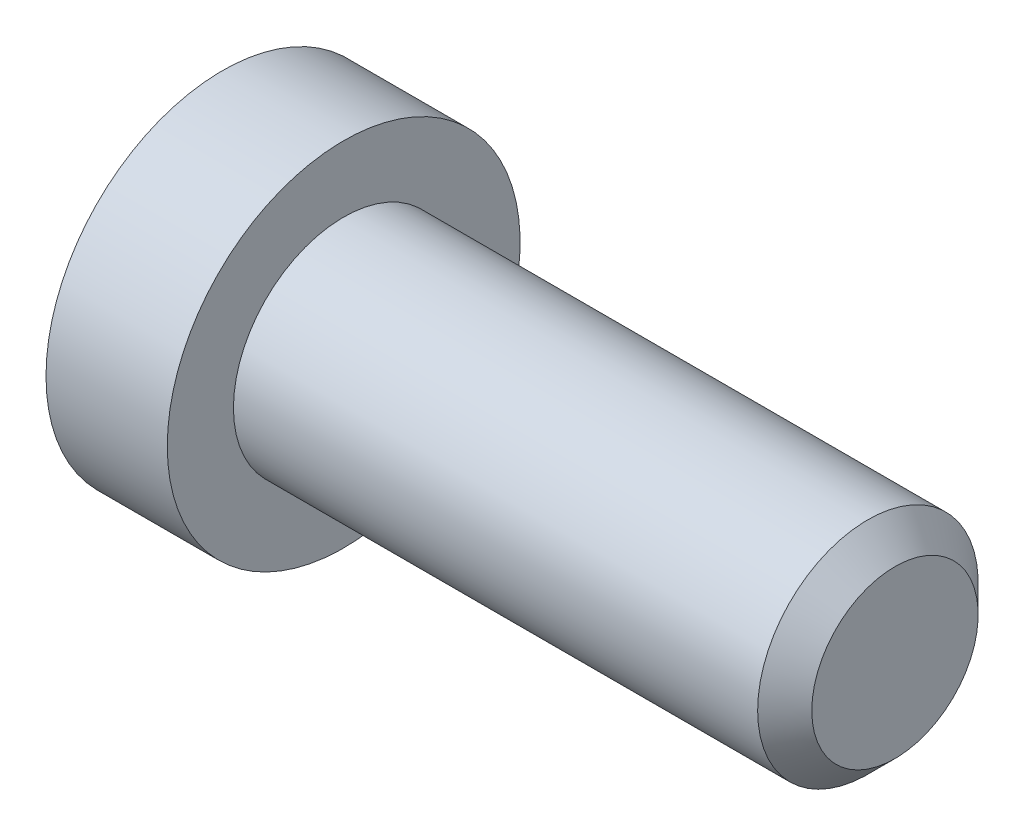
SolidWorks part; units mm, degrees
material "AISI 304"
ref_plane "正面" through (0, 0, 0) normal (0, 0, 1) x (1, 0, 0)
ref_plane "平面" through (0, 0, 0) normal (0, 1, 0) x (1, 0, 0)
ref_plane "右側面" through (0, 0, 0) normal (1, 0, 0) x (0, 0, -1)
ref_plane "Plane1" through (0, 0, 0) normal (0, 0, 1) x (1, 0, 0)
sketch "Sketch1" plane through (0, 0, 0) normal (0, 0, 1) x (1, 0, 0)
  line L0 (0, 0) -> (0, 1)
  line L1 (0, 1) -> (4.7545, 1)
  line L2 (4.7545, 1) -> (5, 0.7545)
  line L3 (5, 0.7545) -> (5, 0)
  line L4 (5, 0) -> (0, 0)
  line L5 (5, 0) -> (0, 0) construction
revolve "Revolve1" add sketch "Sketch1" angle 360 about L5
cosmetic thread "Cosmetic Thread1" parameters "D1"=3.8, "D2"=1.509
ref_plane "Plane2" through (0, 0, 0) normal (0, 0, 1) x (1, 0, 0)
sketch "Sketch2" plane through (0, 0, 0) normal (0, 0, 1) x (1, 0, 0)
  line L0 (-1.1, 0) -> (-1.1, 1.6)
  line L1 (-1.1, 1.6) -> (0, 1.6)
  line L2 (0, 1.6) -> (0, 0)
  line L3 (0, 0) -> (-1.1, 0)
  line L4 (0, 0) -> (-1.1, 0) construction
revolve "Revolve2" add sketch "Sketch2" angle 360 about L4
ref_plane "Plane3" through (0, 0, 0) normal (0, 0, 1) x (1, 0, 0)
sketch "Sketch3" plane through (0, 0, 0) normal (0, 0, 1) x (1, 0, 0)
  line L0 (-1.1, 0) -> (-1.1, 0.78)
  line L1 (-1.1, 0.78) -> (-0.97, 0.65)
  line L2 (-0.97, 0.65) -> (0.1, 0.65)
  line L3 (0.1, 0.65) -> (0.4753, 0)
  line L4 (0.4753, 0) -> (-1.1, 0)
  line L5 (0.4753, 0) -> (-1.1, 0) construction
revolve "Cut-Revolve1" cut sketch "Sketch3" angle 360 about L5
ref_plane "Plane4" through (-1.1, 0, 0) normal (1, 0, 0) x (0, 0, -1)
sketch "Sketch4" plane through (-1.1, 0, 0) normal (1, 0, 0) x (0, 0, -1)
  line L0 (-0.65, -0.3753) -> (0, -0.7506)
  line L1 (0, -0.7506) -> (0.65, -0.3753)
  line L2 (0.65, -0.3753) -> (0.65, 0.3753)
  line L3 (0.65, 0.3753) -> (0, 0.7506)
  line L4 (0, 0.7506) -> (-0.65, 0.3753)
  line L5 (-0.65, 0.3753) -> (-0.65, -0.3753)
extrude "Cut-Extrude1" cut sketch "Sketch4" along normal blind 1.2
